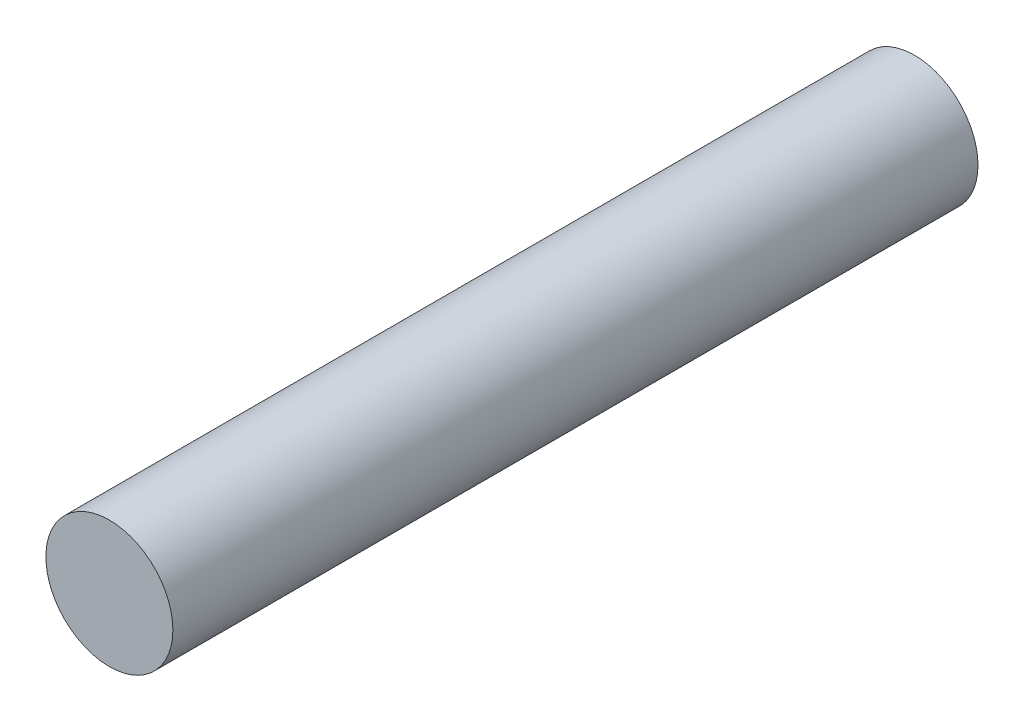
SolidWorks part; units mm, degrees
ref_plane "Front Plane" through (0, 0, 0) normal (0, 0, 1) x (1, 0, 0)
ref_plane "Top Plane" through (0, 0, 0) normal (0, 1, 0) x (1, 0, 0)
ref_plane "Right Plane" through (0, 0, 0) normal (1, 0, 0) x (0, 0, -1)
sketch "Sketch1" plane through (0, 0, 0) normal (0, 0, 1) x (1, 0, 0)
  circle A0 centre (0, 0) radius 2.5
  dimension "D1" = 5
extrude "Boss-Extrude1" add sketch "Sketch1" along normal blind 31.7
